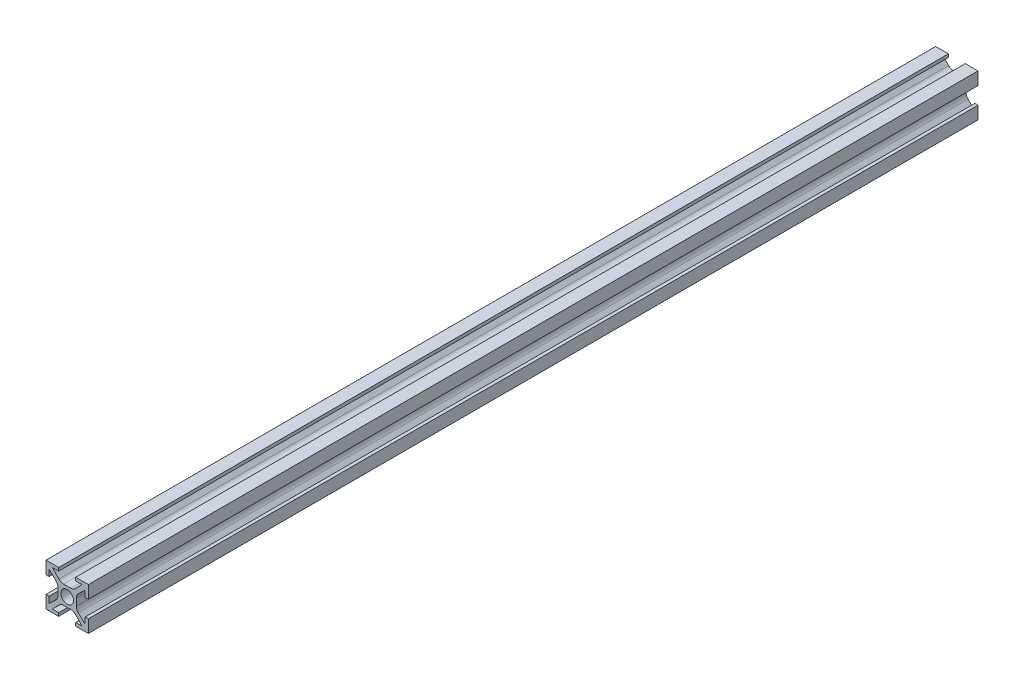
SolidWorks part; units mm, degrees
ref_plane "Plano frontal" through (0, 0, 0) normal (0, 0, 1) x (1, 0, 0)
ref_plane "Plano superior" through (0, 0, 0) normal (0, 1, 0) x (1, 0, 0)
ref_plane "Plano direito" through (0, 0, 0) normal (1, 0, 0) x (0, 0, -1)
sketch "Esboço1" plane through (0, 0, 0) normal (0, 0, 1) x (1, 0, 0)
  line L1 (10, -10) -> (-10, -10)
  line L2 (10, -10) -> (10, 10)
  line L3 (10, 10) -> (-10, 10)
  line L4 (-10, -10) -> (-10, 10)
  line L5 (10, -10) -> (-10, 10) construction
  line L6 (10, 10) -> (-10, -10) construction
  point P0 (0, 0)
  dimension "D1" = 20
  dimension "D2" = 20
extrude "Ressalto-extrusão1" add sketch "Esboço1" along normal blind 420
sketch "Esboço2" plane through (0, 0, 0) normal (0, 0, -1) x (-1, 0, 0)
  line L0 (-12.8371, 0) -> (13.0052, 0) construction
  line L1 (0, -11.8561) -> (0, 11.8) construction
  line L2 (-10, 4) -> (-8.5, 4)
  line L3 (-10, -10) -> (-10, 10) construction
  line L4 (-8.5, 4) -> (-8.5, 7)
  line L5 (-8.5, 7) -> (-4.3538, 3)
  line L6 (-4.3538, 3) -> (-4.3538, -3)
  line L7 (-10, 4) -> (-10, -4)
  line L8 (-8.5, -7) -> (-4.3538, -3)
  line L9 (-8.5, -4) -> (-8.5, -7)
  line L10 (-10, -4) -> (-8.5, -4)
  line L11 (4, 10) -> (4, 8.5)
  line L12 (4, 8.5) -> (7, 8.5)
  line L13 (7, 8.5) -> (3, 4.3538)
  line L14 (3, 4.3538) -> (-3, 4.3538)
  line L15 (4, 10) -> (-4, 10)
  line L16 (-7, 8.5) -> (-3, 4.3538)
  line L17 (-4, 8.5) -> (-7, 8.5)
  line L18 (-4, 10) -> (-4, 8.5)
  line L19 (10, -4) -> (8.5, -4)
  line L20 (8.5, -4) -> (8.5, -7)
  line L21 (8.5, -7) -> (4.3538, -3)
  line L22 (4.3538, -3) -> (4.3538, 3)
  line L23 (10, -4) -> (10, 4)
  line L24 (8.5, 7) -> (4.3538, 3)
  line L25 (8.5, 4) -> (8.5, 7)
  line L26 (10, 4) -> (8.5, 4)
  line L27 (-4, -10) -> (-4, -8.5)
  line L28 (-4, -8.5) -> (-7, -8.5)
  line L29 (-7, -8.5) -> (-3, -4.3538)
  line L30 (-3, -4.3538) -> (3, -4.3538)
  line L31 (-4, -10) -> (4, -10)
  line L32 (7, -8.5) -> (3, -4.3538)
  line L33 (4, -8.5) -> (7, -8.5)
  line L34 (4, -10) -> (4, -8.5)
  circle A0 centre (0, 0) radius 3
  point P17 (-4.3538, 0)
  point P20 (-10, 0)
  point P28 (0, 4.3538)
  point P31 (0, 10)
  point P38 (4.3538, 0)
  point P41 (10, 0)
  point P48 (0, -4.3538)
  point P51 (0, -10)
  dimension "D1" = 6
  dimension "D2" = 4
  dimension "D3" = 3
  dimension "D4" = 1.5
  dimension "D5" = 3
  dimension "D6" = 4
extrude "Corte-extrusão1" cut sketch "Esboço2" against normal through all both and the other way through all
fillet "Filete1" radius 3 8 edges at (-3, -4.3538, 210) (3, -4.3538, 210) (4.3538, -3, 210) (4.3538, 3, 210) (-4.3538, -3, 210) (-4.3538, 3, 210) (-3, 4.3538, 210) (3, 4.3538, 210)
